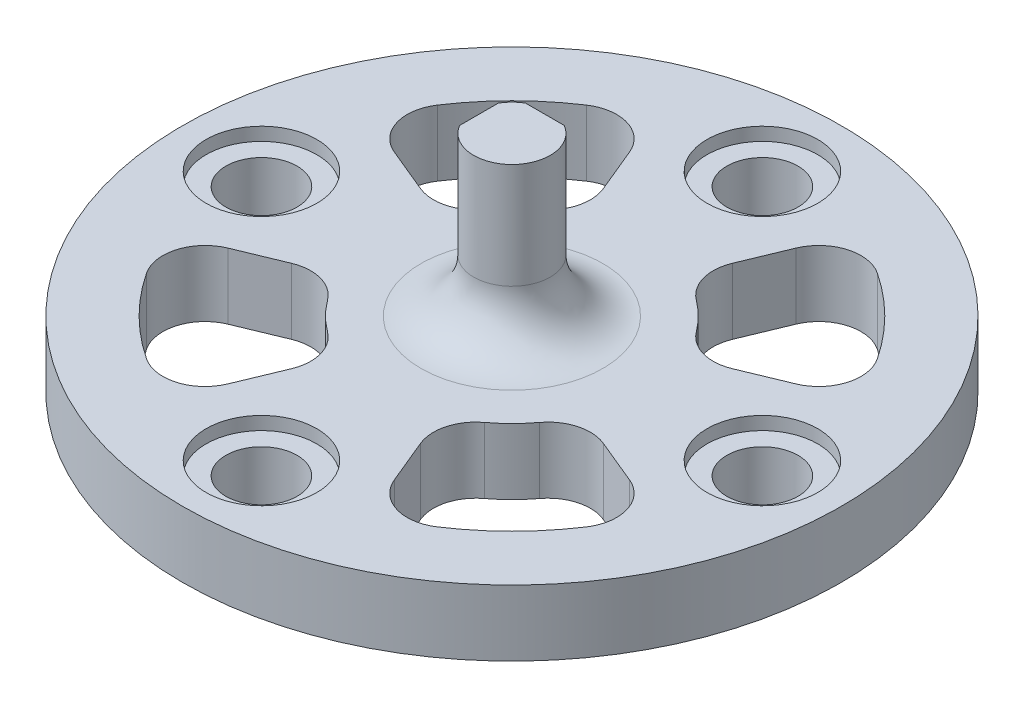
SolidWorks part; units mm, degrees
ref_plane "Front Plane" through (0, 0, 0) normal (0, 0, 1) x (1, 0, 0)
ref_plane "Top Plane" through (0, 0, 0) normal (0, 1, 0) x (1, 0, 0)
ref_plane "Right Plane" through (0, 0, 0) normal (1, 0, 0) x (0, 0, -1)
sketch "Sketch1" plane through (0, 0, 0) normal (0, 1, 0) x (1, 0, 0)
  circle A0 centre (0, 0) radius 12.5
  dimension "D1" = 25
extrude "Boss-Extrude1" add sketch "Sketch1" along normal blind 2.5
sketch "Sketch2" plane through (0, 2.5, 0) normal (0, 1, 0) x (1, 0, 0)
  circle A0 centre (0, 0) radius 9.5 construction
  circle A1 centre (0, 9.5) radius 1.35
  dimension "D1" = 19
  dimension "D2" = 2.7
extrude "Cut-Extrude1" cut sketch "Sketch2" against normal through all
sketch "Sketch4" plane through (0, 2.5, 0) normal (0, 1, 0) x (1, 0, 0)
  circle A0 centre (0, 9.5) radius 2.1
  dimension "D1" = 4.2
extrude "Cut-Extrude2" cut sketch "Sketch4" against normal blind 0.5
sketch "Sketch5" plane through (0, 2.5, 0) normal (0, 1, 0) x (1, 0, 0)
  line L0 (3.8268, 9.2388) -> (0, 0) construction
  line L1 (0, 0) -> (9.2388, 3.8268) construction
  line L2 (1.9134, 4.6194) -> (3.8268, 9.2388)
  line L3 (4.6194, 1.9134) -> (9.2388, 3.8268)
  line L4 (-1000, 0) -> (49000, 0) construction
  arc A0 (3.8268, 9.2388) -> (9.2388, 3.8268) centre (0, 0) cw
  arc A1 (1.9134, 4.6194) -> (4.6194, 1.9134) centre (0, 0) cw
  circle A2 centre (0, 0) radius 12.5 construction
  dimension "D1" = 2.5
  dimension "D2" = 5
  dimension "D3" = 45
  dimension "D4" = 22.5
extrude "Cut-Extrude3" cut sketch "Sketch5" against normal through all
fillet "Fillet3" radius 1.6 4 edges at (4.6194, 1.25, -1.9134) (9.2388, 1.25, -3.8268) (1.9134, 1.25, -4.6194) (3.8268, 1.25, -9.2388)
pattern_circular "CirPattern1" count 4 over 360 about axis through (0, 0, 0) along (0, 1, 0) of "Cut-Extrude1", "Cut-Extrude2", "Cut-Extrude3", "Fillet3"
sketch "Sketch3" plane through (0, 2.5, 0) normal (0, 1, 0) x (1, 0, 0)
  circle A0 centre (0, 0) radius 1.45
  dimension "D1" = 2.9
extrude "Boss-Extrude2" add sketch "Sketch3" along normal blind 6
fillet "Fillet2" radius 2 1 edges at (0, 2.5, 1.45)
sketch "Sketch6" plane through (0, 8.5, 0) normal (0, 1, 0) x (1, 0, 0)
  line L0 (0, 0) -> (0, 1.25) construction
  line L1 (-0.7348, 1.25) -> (0.7348, 1.25)
  line L2 (-0.7348, 1.25) -> (-0.7348, 1.65)
  line L3 (-0.7348, 1.65) -> (0.7348, 1.65)
  line L4 (0.7348, 1.25) -> (0.7348, 1.65)
  line L5 (-0.7348, 1.25) -> (0.7348, 1.65) construction
  line L6 (-0.7348, 1.65) -> (0.7348, 1.25) construction
  line L7 (-1.25, -0.7348) -> (-1.65, -0.7348)
  line L8 (-1.25, -0.7348) -> (-1.25, 0.7348)
  line L9 (-1.25, 0.7348) -> (-1.65, 0.7348)
  line L10 (-1.65, -0.7348) -> (-1.65, 0.7348)
  line L11 (-1.25, -0.7348) -> (-1.65, 0.7348) construction
  line L12 (-1.25, 0.7348) -> (-1.65, -0.7348) construction
  line L13 (0, 0) -> (-1.25, 0) construction
  circle A0 centre (0, 0) radius 1.45 construction
  circle A1 centre (0, 0) radius 1.45 construction
  point P0 (0, 1.45)
  point P9 (-1.45, 0)
  dimension "D1" = 1.25
  dimension "D2" = 1.25
extrude "Cut-Extrude4" cut sketch "Sketch6" against normal blind 4
